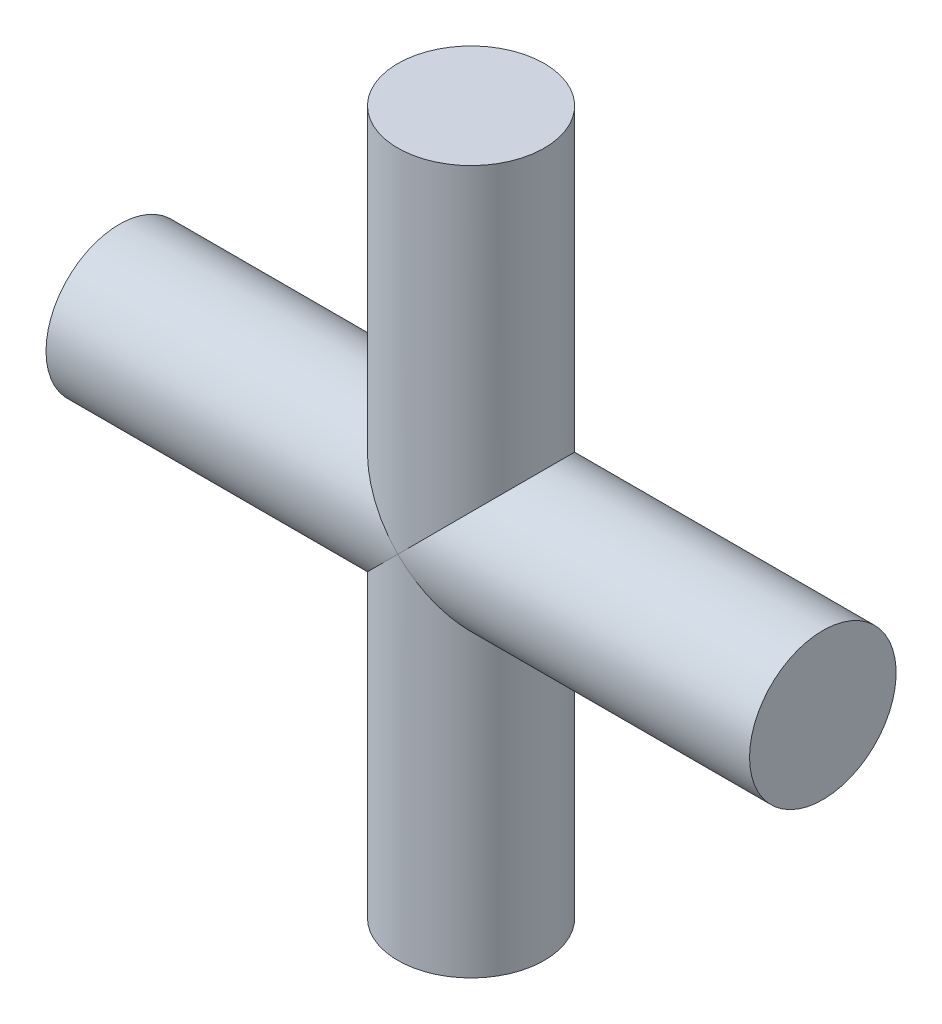
SolidWorks part; units mm, degrees
ref_plane "Front Plane" through (0, 0, 0) normal (0, 0, 1) x (1, 0, 0)
ref_plane "Top Plane" through (0, 0, 0) normal (0, 1, 0) x (1, 0, 0)
ref_plane "Right Plane" through (0, 0, 0) normal (1, 0, 0) x (0, 0, -1)
sketch "草图4" plane through (0, 0, 0) normal (0, 1, 0) x (1, 0, 0)
  line L0 (0, 0) -> (1.2, 0)
  line L1 (1.2, 0) -> (1.2, -0.25)
  line L2 (1.2, -0.25) -> (-1.2, -0.25)
  line L3 (-1.2, -0.25) -> (-1.2, 0)
  line L4 (-1.2, 0) -> (0, 0)
revolve "旋转5" add sketch "草图4" angle 360 about L4
sketch "草图5" plane through (0, 0, 0) normal (0, 0, 1) x (1, 0, 0)
  line L0 (0, 0) -> (0, 1.2)
  line L1 (0, 1.2) -> (0.25, 1.2)
  line L2 (0.25, 1.2) -> (0.25, -1.2)
  line L3 (0.25, -1.2) -> (0, -1.2)
  line L4 (0, -1.2) -> (0, 0)
revolve "旋转6" add sketch "草图5" angle 360 about L0
sketch "草图6" plane through (0, 0, 0) normal (0, 1, 0) x (1, 0, 0)
  line L1 (-0.3, -0.3) -> (0.3, -0.3)
  line L2 (-0.3, -0.3) -> (-0.3, 0.3)
  line L3 (-0.3, 0.3) -> (0.3, 0.3)
  line L4 (0.3, -0.3) -> (0.3, 0.3)
  line L5 (0, 0.3) -> (0, -0.3) construction
  line L6 (-0.3, 0) -> (0.3, 0) construction
  point P0 (0, 0)
sketch "草图7" plane through (0, 0, 0) normal (1, 0, 0) x (0, 0, -1)
  line L6 (-0.3, -0.3) -> (0.3, -0.3)
  line L7 (-0.3, -0.3) -> (-0.3, 0.3)
  line L8 (-0.3, 0.3) -> (0.3, 0.3)
  line L9 (0.3, -0.3) -> (0.3, 0.3)
  line L10 (0, 0.3) -> (0, -0.3) construction
  line L11 (-0.3, 0) -> (0.3, 0) construction
  point P0 (0, 0)
